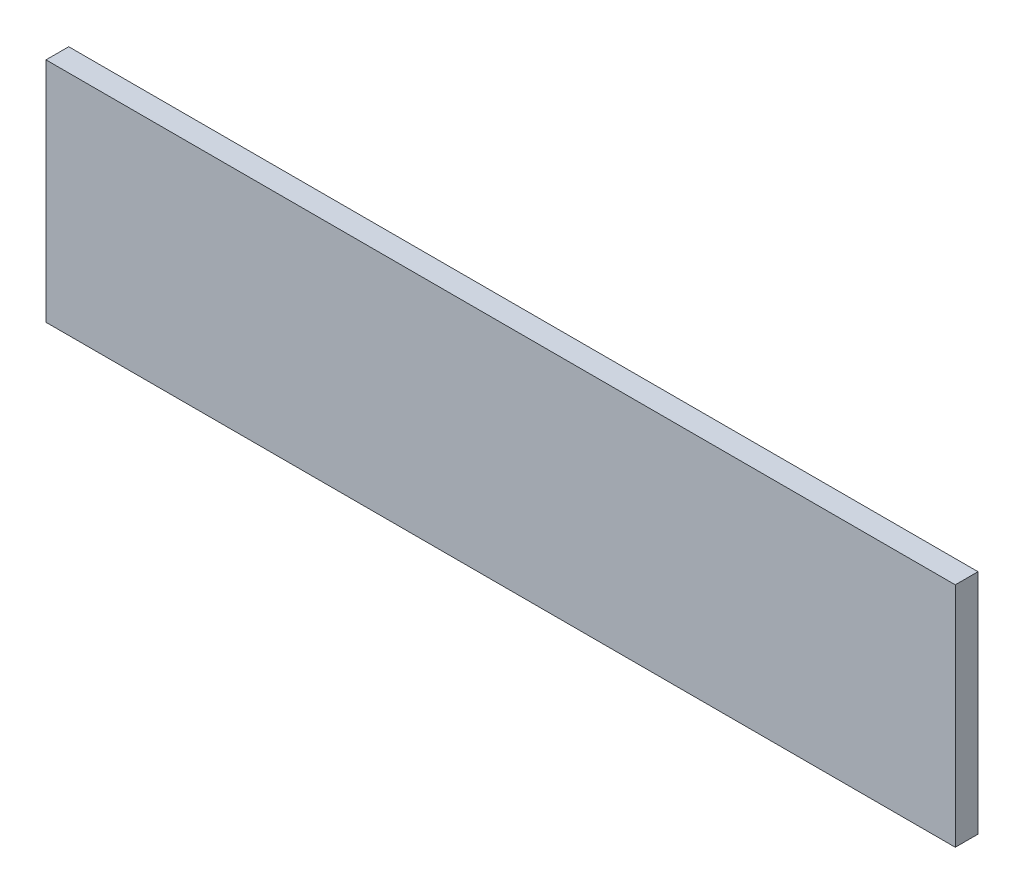
SolidWorks part; units mm, degrees
ref_plane "Front Plane" through (0, 0, 0) normal (0, 0, 1) x (1, 0, 0)
ref_plane "Top Plane" through (0, 0, 0) normal (0, 1, 0) x (1, 0, 0)
ref_plane "Right Plane" through (0, 0, 0) normal (1, 0, 0) x (0, 0, -1)
sketch "Sketch1" plane through (0, 0, 0) normal (0, 0, 1) x (1, 0, 0)
  line L1 (-200, 50) -> (200, 50)
  line L2 (-200, 50) -> (-200, -50)
  line L3 (-200, -50) -> (200, -50)
  line L4 (200, 50) -> (200, -50)
  dimension "D1" = 400
  dimension "D2" = 100
  dimension "D3" = 200
  dimension "D4" = 50
extrude "Boss-Extrude1" add sketch "Sketch1" along normal blind 10
sketch "Sketch2" plane through (0, 0, 0) normal (0, 0, -1) x (-1, 0, 0)
  circle A0 centre (0, 0) radius 20
  dimension "D1" = 40
extrude "Cut-Extrude1" cut sketch "Sketch2" against normal blind 0.5
